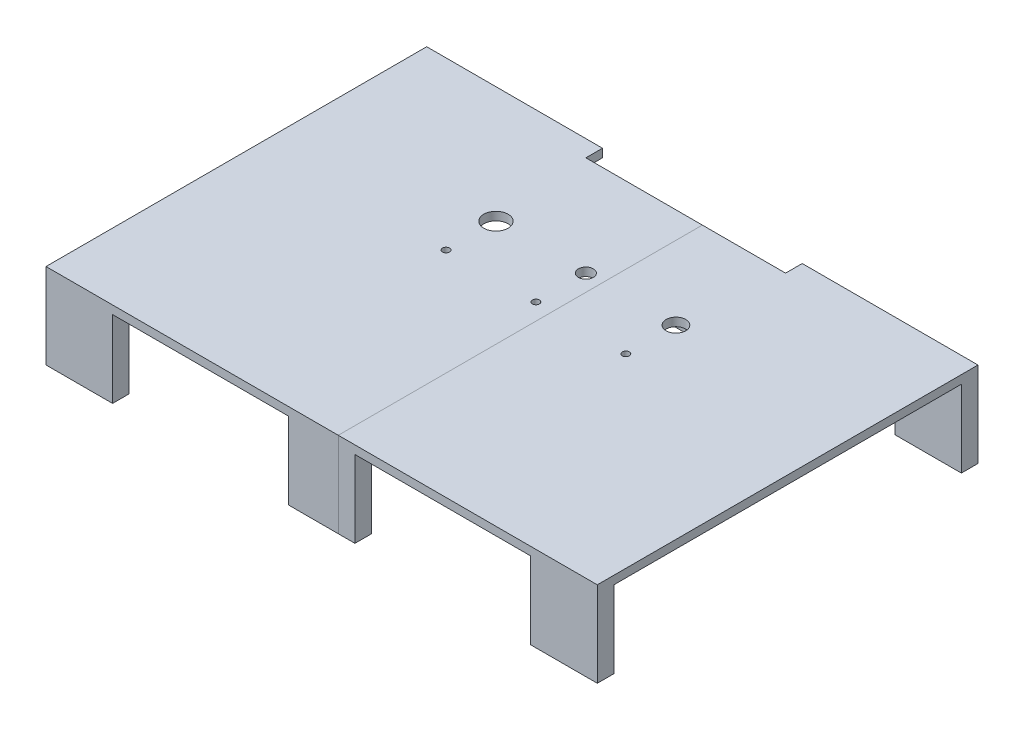
SolidWorks part; units mm, degrees
ref_plane "Front Plane" through (0, 0, 0) normal (0, 0, 1) x (1, 0, 0)
ref_plane "Top Plane" through (0, 0, 0) normal (0, 1, 0) x (1, 0, 0)
ref_plane "Right Plane" through (0, 0, 0) normal (1, 0, 0) x (0, 0, -1)
sketch "Sketch1" plane through (0, 0, 0) normal (0, 1, 0) x (1, 0, 0)
  line L1 (-210.3438, -145.2563) -> (210.3438, -145.2563)
  line L2 (-210.3438, -145.2563) -> (-210.3438, 145.2562)
  line L3 (-210.3438, 145.2562) -> (210.3438, 145.2562)
  line L4 (210.3438, -145.2563) -> (210.3438, 145.2562)
  line L5 (-210.3438, -145.2563) -> (210.3438, 145.2562) construction
  line L6 (-210.3438, 145.2562) -> (210.3438, -145.2563) construction
  point P0 (0, 0)
  dimension "D1" = 420.6875
  dimension "D2" = 290.5125
extrude "Desktop" add sketch "Sketch1" along normal blind 6.35
sketch "Sketch5" plane through (0, 6.35, 0) normal (0, 1, 0) x (1, 0, 0)
  line L0 (210.3438, 145.2562) -> (-210.3438, 145.2562) construction
  line L1 (-76.2, 132.5562) -> (76.2, 132.5562)
  line L2 (-76.2, 132.5562) -> (-76.2, 145.2562)
  line L3 (-76.2, 145.2562) -> (76.2, 145.2562)
  line L4 (76.2, 132.5562) -> (76.2, 145.2562)
  line L5 (-76.2, 132.5562) -> (76.2, 145.2562) construction
  line L6 (-76.2, 145.2562) -> (76.2, 132.5562) construction
  point P0 (0, 138.9062)
  dimension "D1" = 152.4
  dimension "D2" = 12.7
extrude "HDMI Screen Cutout" cut sketch "Sketch5" against normal blind 16.51
sketch "Sketch8" plane through (0, 6.35, 0) normal (0, 1, 0) x (1, 0, 0)
  line L0 (210.3438, -145.2563) -> (210.3438, 145.2562) construction
  line L1 (-210.3438, 145.2562) -> (-210.3438, -145.2563) construction
  line L2 (-76.2, 145.2562) -> (-210.3438, 145.2562) construction
  circle A0 centre (68.7387, 56.3562) radius 7.493
  circle A1 centre (-68.6118, 56.3562) radius 9.271
  circle A2 centre (0, 56.3562) radius 5.715
  circle A3 centre (-68.6118, 18.2562) radius 2.667
  circle A6 centre (0, 18.2563) radius 2.667
  circle A7 centre (68.6118, 18.2563) radius 2.667
  dimension "D2" = 14.986
  dimension "D4" = 18.542
  dimension "D6" = 11.43
  dimension "D8" = 5.334
  dimension "D1" = 141.605
  dimension "D3" = 141.732
  dimension "D5" = 88.9
  dimension "D9" = 3
  dimension "D7" = 38.1
extrude "Switches and Lights" cut sketch "Sketch8" against normal blind 16.51
sketch "Sketch9" plane through (0, 0, 0) normal (0, -1, 0) x (1, 0, 0)
  line L0 (-210.3438, 145.2563) -> (210.3438, 145.2563) construction
  line L1 (-25.4, 132.5563) -> (25.4, 132.5563)
  line L2 (-25.4, 132.5563) -> (-25.4, 145.2563)
  line L3 (-25.4, 145.2563) -> (25.4, 145.2563)
  line L4 (25.4, 132.5563) -> (25.4, 145.2563)
  line L5 (-25.4, 132.5563) -> (25.4, 145.2563) construction
  line L6 (-25.4, 145.2563) -> (25.4, 132.5563) construction
  line L7 (76.2, -132.5562) -> (-76.2, -132.5562) construction
  line L8 (-210.3438, 145.2563) -> (-159.5437, 145.2563)
  line L9 (-210.3438, 145.2563) -> (-210.3438, 132.5563)
  line L10 (-210.3438, 132.5563) -> (-159.5437, 132.5563)
  line L11 (-159.5437, 145.2563) -> (-159.5437, 132.5563)
  line L12 (-210.3438, -145.2562) -> (-159.5437, -145.2562)
  line L13 (-210.3438, -145.2562) -> (-210.3438, -132.5562)
  line L14 (-210.3438, -132.5562) -> (-159.5437, -132.5562)
  line L15 (-159.5437, -145.2562) -> (-159.5437, -132.5562)
  line L16 (210.3438, -145.2562) -> (159.5437, -145.2562)
  line L17 (210.3438, -145.2562) -> (210.3438, -132.5562)
  line L18 (210.3438, -132.5562) -> (159.5437, -132.5562)
  line L19 (159.5437, -145.2562) -> (159.5437, -132.5562)
  line L20 (210.3438, 145.2563) -> (159.5437, 145.2563)
  line L21 (210.3438, 145.2563) -> (210.3438, 132.5563)
  line L22 (210.3438, 132.5563) -> (159.5437, 132.5563)
  line L23 (159.5437, 145.2563) -> (159.5437, 132.5563)
  line L24 (-25.4, -132.5562) -> (25.4, -132.5562)
  line L25 (-25.4, -132.5562) -> (-25.4, -119.8562)
  line L26 (-25.4, -119.8562) -> (25.4, -119.8562)
  line L27 (25.4, -132.5562) -> (25.4, -119.8562)
  point P0 (0, 138.9063)
  dimension "D1" = 50.8
  dimension "D2" = 12.7
  dimension "D3" = 50.8
  dimension "D4" = 12.7
  dimension "D5" = 50.8
  dimension "D6" = 12.7
  dimension "D7" = 50.8
  dimension "D8" = 50.8
  dimension "D9" = 50.8
  dimension "D10" = 12.7
  dimension "D11" = 12.7
  dimension "D12" = 12.7
extrude "Boss-Extrude1" add sketch "Sketch9" along normal blind 58.7375
ref_plane "Plane1" through (12.7, 0, 0) normal (1, 0, 0) x (0, 0, -1)
split "Split2" trim tools "Plane1" bodies to split 109 resulting bodies 112 113
